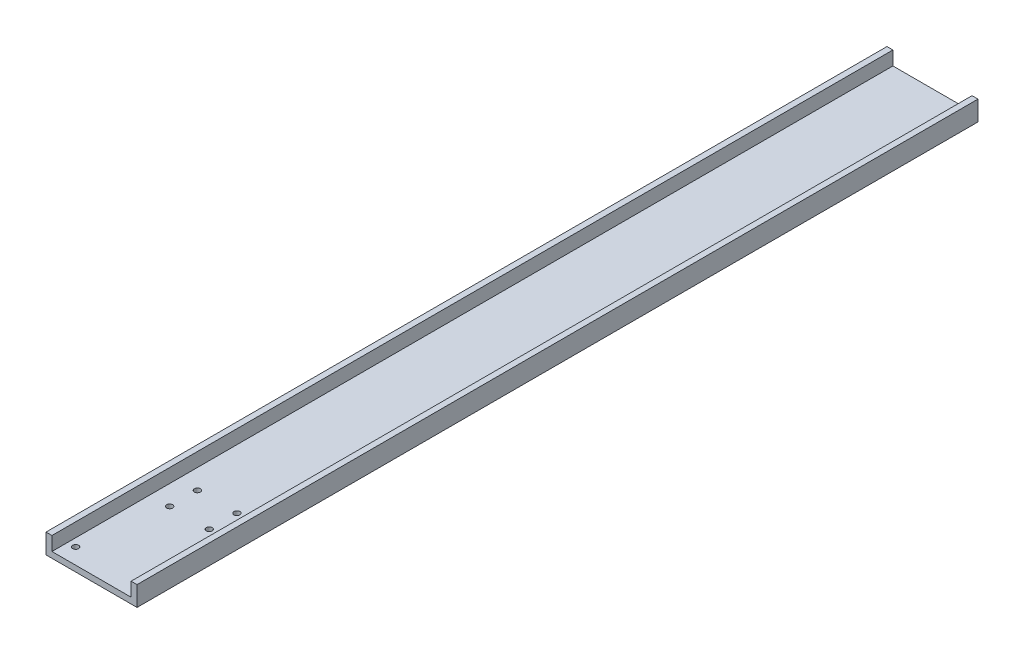
SolidWorks part; units mm, degrees
ref_plane "Front Plane" through (0, 0, 0) normal (0, 0, 1) x (1, 0, 0)
ref_plane "Top Plane" through (0, 0, 0) normal (0, 1, 0) x (1, 0, 0)
ref_plane "Right Plane" through (0, 0, 0) normal (1, 0, 0) x (0, 0, -1)
sketch "Sketch1" plane through (0, 0, 0) normal (0, 0, 1) x (1, 0, 0)
  line L0 (0, 0) -> (0, 7)
  line L1 (0, 7) -> (-3, 7)
  line L2 (-3, 7) -> (-3, -3)
  line L3 (-3, -3) -> (43, -3)
  line L4 (43, -3) -> (43, 7)
  line L5 (43, 7) -> (40, 7)
  line L6 (40, 7) -> (40, 0)
  line L7 (40, 0) -> (0, 0)
  dimension "D1" = 3
  dimension "D2" = 3
  dimension "D3" = 3
  dimension "D4" = 10
  dimension "D5" = 40
extrude "Boss-Extrude1" add sketch "Sketch1" along normal blind 425 contours L7 L0 L1 L2 L3 L4 L5 L6
hole_wizard "Ø3.0mm Dowel Hole1" positions "Sketch3" profile "Sketch2" hole size "Ø3.0" standard "ISO"
sketch "Sketch3" plane through (0, 0, 0) normal (0, 1, 0) x (1, 0, 0)
  line L0 (-3, -425) -> (-3, 0) construction
  line L1 (40, -425) -> (0, -425) construction
  point P0 (10, -375.5)
  point P2 (30, -375.5)
  point P4 (30, -361.5)
  point P6 (10, -361.5)
  dimension "D1" = 20
  dimension "D2" = 14
  dimension "D3" = 13
  dimension "D4" = 49.5
sketch "Sketch2" plane through (10, 0, 375.5) normal (1, 0, 0) x (0, 0, 1)
  line L0 (0, 0) -> (0, 15.9013)
  line L1 (0, 15.9013) -> (1.5, 15)
  line L2 (1.5, 15) -> (1.5, 0)
  line L5 (1.5, 0) -> (0, 0)
  line L10 (0, 15.9013) -> (-1.5, 15) construction
  line L11 (0, -6.35) -> (0, 107.95) construction
  dimension "Hole Dia." = 3
  dimension "Hole Depth" = 15
  dimension "Drill Angle" = 118
hole_wizard "Ø3.0mm Dowel Hole2" positions "Sketch5" profile "Sketch4" hole size "Ø3.0" standard "ISO"
sketch "Sketch5" plane through (0, -3, 0) normal (0, -1, 0) x (-1, 0, 0)
  line L0 (3, -425) -> (3, 0) construction
  line L1 (3, -425) -> (-43, -425) construction
  point P0 (-36, -417)
  point P2 (-4, -417)
  dimension "D1" = 32
  dimension "D2" = 7
  dimension "D3" = 8
sketch "Sketch4" plane through (36, -3, 417) normal (1, 0, 0) x (0, 0, -1)
  line L0 (0, 0) -> (0, 15.9013)
  line L1 (0, 15.9013) -> (1.5, 15)
  line L2 (1.5, 15) -> (1.5, 0)
  line L5 (1.5, 0) -> (0, 0)
  line L10 (0, 15.9013) -> (-1.5, 15) construction
  line L11 (0, -6.35) -> (0, 107.95) construction
  dimension "Hole Dia." = 3
  dimension "Hole Depth" = 15
  dimension "Drill Angle" = 118
